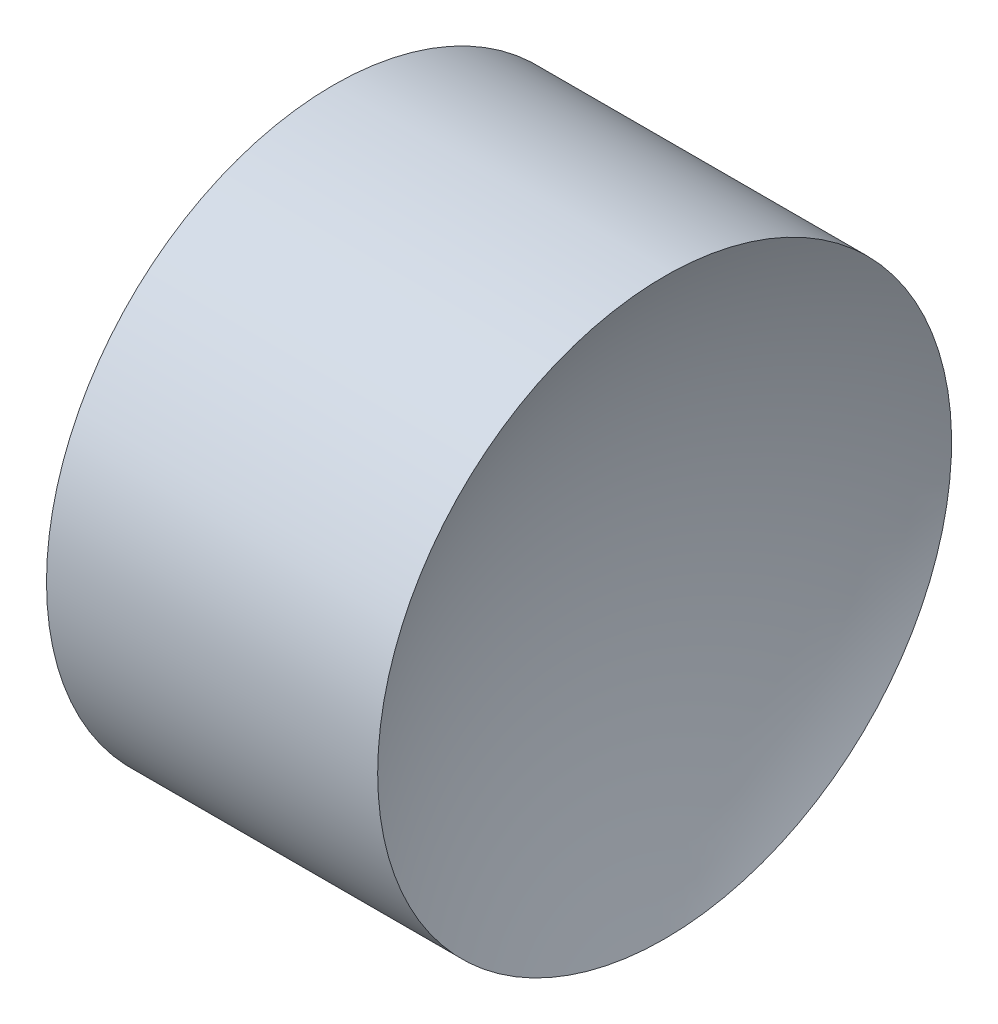
SolidWorks part; units mm, degrees
ref_plane "前视基准面" through (0, 0, 0) normal (0, 0, 1) x (1, 0, 0)
ref_plane "上视基准面" through (0, 0, 0) normal (0, 1, 0) x (1, 0, 0)
ref_plane "右视基准面" through (0, 0, 0) normal (1, 0, 0) x (0, 0, -1)
sketch "草图1" plane through (0, 0, 0) normal (0, 0, 1) x (1, 0, 0)
  line L0 (10.6125, 6.5223) -> (13.9161, 6.5223) construction
  line L1 (11.5141, 6.5223) -> (12.5141, 6.5223)
  line L3 (12.0141, 8.0223) -> (12.8797, 8.0223)
  line L4 (12.0141, 8.0223) -> (11.1485, 8.0223)
  arc A0 (12.8797, 8.0223) -> (12.5141, 6.5223) centre (15.7741, 6.5223) ccw
  arc A1 (11.5141, 6.5223) -> (11.1485, 8.0223) centre (8.2541, 6.5223) ccw
revolve "旋转1" add sketch "草图1" angle 360 about L0
